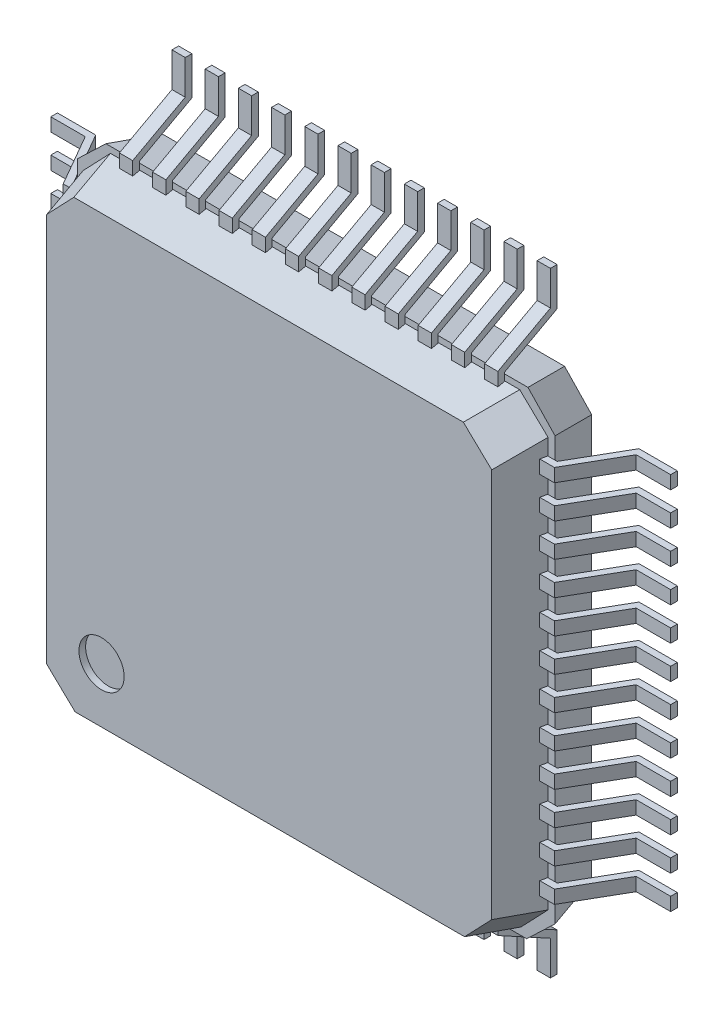
SolidWorks part; units mm, degrees
ref_plane "Front Plane" through (0, 0, 0) normal (0, 0, 1) x (1, 0, 0)
ref_plane "Top Plane" through (0, 0, 0) normal (0, 1, 0) x (1, 0, 0)
ref_plane "Right Plane" through (0, 0, 0) normal (1, 0, 0) x (0, 0, -1)
sketch "Sketch1" plane through (0, 0, 0) normal (0, 0, 1) x (1, 0, 0)
  line L1 (0, 0) -> (7, 0)
  line L2 (0, 0) -> (0, 7)
  line L3 (0, 7) -> (7, 7)
  line L4 (7, 0) -> (7, 7)
  dimension "D1" = 7
  dimension "D2" = 7
extrude "Boss-Extrude1" add sketch "Sketch1" along normal blind 0.7 draft 12
chamfer "Chamfer1" distance 0.4 angle 45 4 edges at (0.0744, 6.9256, 0.35) (0.0744, 0.0744, 0.35) (6.9256, 0.0744, 0.35) (6.9256, 6.9256, 0.35)
sketch "Sketch2" plane through (0, 0, 0) normal (0, 0, 1) x (1, 0, 0)
  line L1 (-0.0867, -0.1104) -> (7.1055, -0.1104)
  line L2 (-0.0867, -0.1104) -> (-0.0867, 7.0916)
  line L3 (-0.0867, 7.0916) -> (7.1055, 7.0916)
  line L4 (7.1055, -0.1104) -> (7.1055, 7.0916)
  line L5 (-0.0867, -0.1104) -> (7.1055, 7.0916) construction
  line L6 (-0.0867, 7.0916) -> (7.1055, -0.1104) construction
  point P0 (3.5094, 3.4906)
extrude "Boss-Extrude2" add sketch "Sketch2" against normal blind 0.7 draft 12
chamfer "Chamfer3" distance 0.4 angle 45 4 edges at (7.0311, -0.036, -0.35) (-0.0123, -0.036, -0.35) (-0.0123, 7.0172, -0.35) (7.0311, 7.0172, -0.35)
ref_plane "Plane2" through (3.25, 0, 0) normal (1, 0, 0) x (0, 0, -1)
sketch "Sketch3" plane through (3.25, 0, 0) normal (1, 0, 0) x (0, 0, -1)
  line L0 (-0.0561, 6.9409) -> (-0.0561, 7.1494)
  line L1 (-0.0561, 7.1494) -> (0.7351, 7.5804)
  line L3 (0.7351, 7.5804) -> (0.7351, 8.1284)
  dimension "D3" = 0.7912
extrude "Extrude-Thin1" add sketch "Sketch3" along normal mid plane 0.2 thin thin type mid plane wall 0.1
pattern_linear "LPattern1" count 7 spacing 0.5 along (1, 0, 0) count 6 spacing 0.5 along (-1, 0, 0) of "Extrude-Thin1"
ref_plane "Plane3" through (0, 3.5, 0) normal (0, 1, 0) x (1, 0, 0)
mirror "Mirror2" about plane through (0, 3.5, 0) normal (0, 1, 0) of "LPattern1", "Extrude-Thin1"
ref_plane "Plane4" through (0, 3.75, 0) normal (0, 1, 0) x (1, 0, 0)
sketch "Sketch5" plane through (0, 3.75, 0) normal (0, 1, 0) x (1, 0, 0)
  line L0 (0.0385, -0.0537) -> (-0.1701, -0.0537)
  line L1 (-0.1701, -0.0537) -> (-0.6201, 0.728)
  line L3 (-0.6201, 0.728) -> (-1.168, 0.728)
  dimension "D3" = 0.45
extrude "Extrude-Thin2" add sketch "Sketch5" along normal mid plane 0.2 thin thin type mid plane wall 0.1
pattern_linear "LPattern2" count 7 spacing 0.5 along (0, -1, 0) count 6 spacing 0.5 along (0, 1, 0) of "Extrude-Thin2"
ref_plane "Plane5" through (3.5, 0, 0) normal (1, 0, 0) x (0, 0, -1)
mirror "Mirror3" about plane through (3.5, 0, 0) normal (1, 0, 0) of "Extrude-Thin2", "LPattern2"
ref_plane "Plane6" through (0, 0, 0.7) normal (0, 0, 1) x (1, 0, 0)
sketch "Sketch6" plane through (0, 0, 0.7) normal (0, 0, 1) x (1, 0, 0)
  circle A0 centre (0.9747, 0.9758) radius 0.3404
extrude "Cut-Extrude2" cut sketch "Sketch6" against normal blind 0.1
